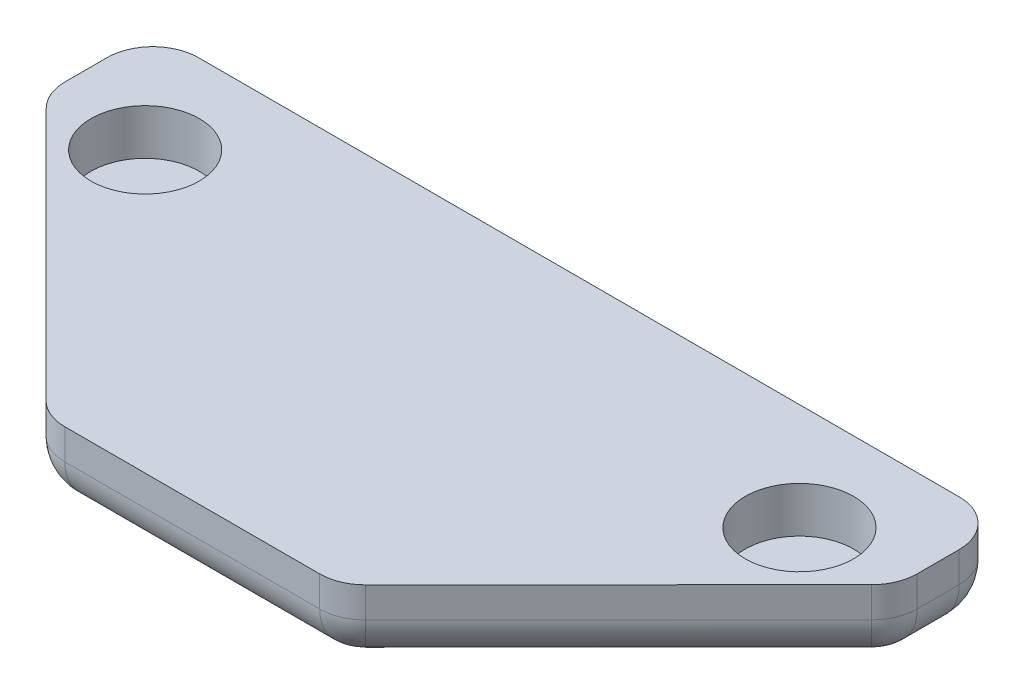
SolidWorks part; units mm, degrees
ref_plane "Front Plane" through (0, 0, 0) normal (0, 0, 1) x (1, 0, 0)
ref_plane "Top Plane" through (0, 0, 0) normal (0, 1, 0) x (1, 0, 0)
ref_plane "Right Plane" through (0, 0, 0) normal (1, 0, 0) x (0, 0, -1)
sketch "Sketch1" plane through (0, 0, 0) normal (0, 1, 0) x (1, 0, 0)
  line L0 (-21.2162, 11.7419) -> (-21.2162, 8.2419)
  line L1 (-21.2162, 8.2419) -> (-12.0249, -0.9581)
  line L2 (-12.0249, -0.9581) -> (-7.2162, -0.9581)
  line L7 (-7.2162, -0.9581) -> (-7.2162, 11.7419)
  line L10 (-7.2162, 11.7419) -> (-21.2162, 11.7419)
  dimension "D2" = 9.2
  dimension "D4" = 14
extrude "Boss-Extrude1" add sketch "Sketch1" along normal blind 2.5
sketch "Sketch2" plane through (0, 2.5, 0) normal (0, 1, 0) x (1, 0, 0)
  line L0 (-17.9662, 11.7419) -> (-17.9662, -0.786) construction
  line L1 (-7.2162, 11.7419) -> (-21.2162, 11.7419) construction
  line L2 (-21.2162, 8.2419) -> (-7.2162, 8.2419) construction
  line L3 (-21.2162, 11.7419) -> (-21.2162, 8.2419) construction
  line L4 (-7.2162, -0.9581) -> (-7.2162, 11.7419) construction
  circle A0 centre (-17.9662, 8.2419) radius 1.78
  dimension "D1" = 3.25
  dimension "D2" = 3.5
extrude "Cut-Extrude1" cut sketch "Sketch2" against normal blind 1.5
fillet "Fillet1" radius 1.5 7 edges at (-12.0249, 1.25, 0.9581) (-21.2162, 1.25, -8.2419) (-21.2162, 1.25, -11.7419) (-9.6205, 0, 0.9581) (-16.6205, 0, -3.6419) (-21.2162, 0, -9.9919) (-14.2162, 0, -11.7419)
mirror "Mirror1" about plane through (-7.2162, 2.5, 0.9581) normal (-1, 0, 0) of bodies 102
